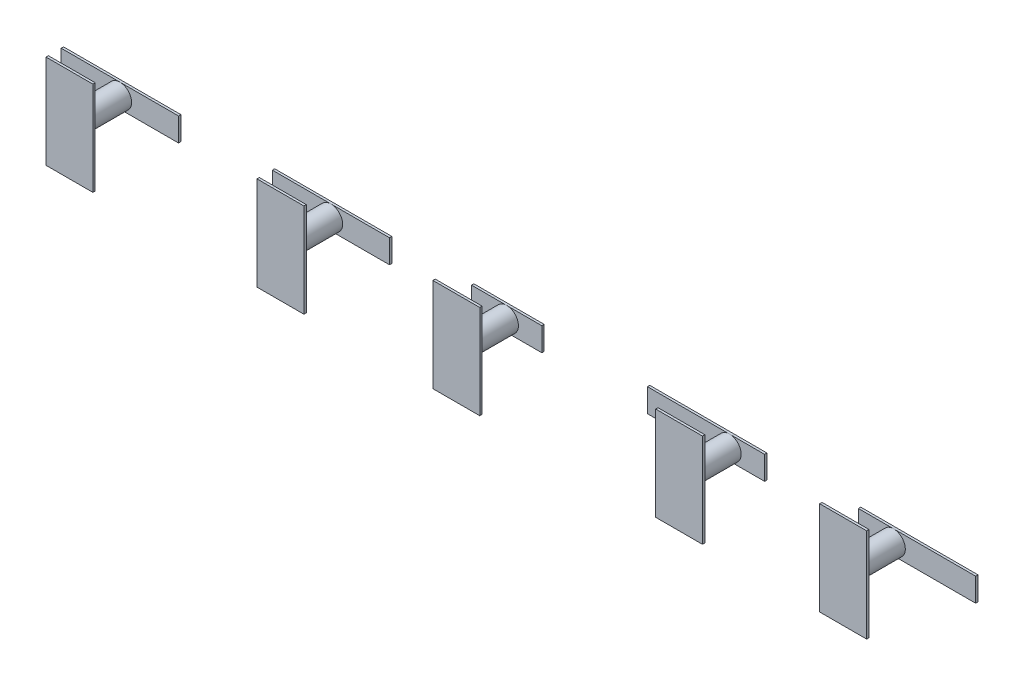
SolidWorks part; units mm, degrees
ref_plane "Front Plane" through (0, 0, 0) normal (0, 0, 1) x (1, 0, 0)
ref_plane "Top Plane" through (0, 0, 0) normal (0, 1, 0) x (1, 0, 0)
ref_plane "Right Plane" through (0, 0, 0) normal (1, 0, 0) x (0, 0, -1)
sketch "Sketch1" plane through (0, 0, 0) normal (0, 0, 1) x (1, 0, 0)
  line L1 (-61, 40) -> (61, 40)
  line L2 (-63, 38) -> (-63, -38)
  line L3 (-61, -40) -> (61, -40)
  line L4 (63, 38) -> (63, -38)
  line L5 (-63, 40) -> (63, -40) construction
  line L6 (-63, -40) -> (63, 40) construction
  arc A0 (61, 40) -> (63, 38) centre (61, 38) cw
  arc A1 (63, -38) -> (61, -40) centre (61, -38) cw
  arc A2 (-61, -40) -> (-63, -38) centre (-61, -38) cw
  arc A3 (-63, 38) -> (-61, 40) centre (-61, 38) cw
  point P0 (0, 0)
  dimension "D1" = 2
sketch "Sketch2" plane through (0, 0, 0) normal (0, 0, 1) x (1, 0, 0)
  line L0 (-5, 5.1169) -> (-5, -5.1169)
  line L1 (-4.2428, -5.5457) -> (4.2854, -0.4287)
  line L2 (4.2854, 0.4287) -> (-4.2428, 5.5457)
  line L3 (-10, -1.5) -> (-10, 1.5)
  line L4 (-10.5, 2) -> (-14, 2)
  line L5 (-14, 2) -> (-14, 5.5)
  line L6 (-14.5, 6) -> (-17.5, 6)
  line L7 (-18, 5.5) -> (-18, 2)
  line L8 (-18, 2) -> (-21.5, 2)
  line L9 (-22, 1.5) -> (-22, -1.5)
  line L10 (-21.5, -2) -> (-18, -2)
  line L11 (-18, -2) -> (-18, -5.5)
  line L12 (-17.5, -6) -> (-14.5, -6)
  line L13 (-14, -5.5) -> (-14, -2)
  line L14 (-14, -2) -> (-10.5, -2)
  line L15 (-28, 1.5) -> (-28, -1.5)
  line L16 (-28.5, -2) -> (-39.5, -2)
  line L17 (-40, -1.5) -> (-40, 1.5)
  line L18 (-39.5, 2) -> (-28.5, 2)
  line L19 (10, 4.5) -> (10, -4.5)
  line L20 (10.5, -5) -> (12.5, -5)
  line L21 (13, -4.5) -> (13, -2)
  line L22 (12.5, 5) -> (10.5, 5)
  line L23 (28, 5.2306) -> (28, -5.2306)
  line L24 (21.2969, 5.6875) -> (13, 2)
  line L25 (13, -2) -> (21.2969, -5.6875)
  line L26 (22, -5.2306) -> (22, 5.2306)
  line L27 (13, 2) -> (13, 4.5)
  line L28 (28.7031, -5.6875) -> (37, -2)
  line L29 (28.7031, 5.6875) -> (37, 2)
  line L30 (37, 2) -> (37, 4.5)
  line L31 (37.5, 5) -> (39.5, 5)
  line L32 (40, 4.5) -> (40, -4.5)
  line L33 (39.5, -5) -> (37.5, -5)
  line L34 (37, -4.5) -> (37, -2)
  arc A0 (-39.5, -2) -> (-40, -1.5) centre (-39.5, -1.5) cw
  arc A1 (-40, 1.5) -> (-39.5, 2) centre (-39.5, 1.5) cw
  arc A2 (-28.5, 2) -> (-28, 1.5) centre (-28.5, 1.5) cw
  arc A3 (-28, -1.5) -> (-28.5, -2) centre (-28.5, -1.5) cw
  arc A4 (-14.5, -6) -> (-14, -5.5) centre (-14.5, -5.5) ccw
  arc A5 (-17.5, -6) -> (-18, -5.5) centre (-17.5, -5.5) cw
  arc A6 (-21.5, -2) -> (-22, -1.5) centre (-21.5, -1.5) cw
  arc A7 (-22, 1.5) -> (-21.5, 2) centre (-21.5, 1.5) cw
  arc A8 (-18, 5.5) -> (-17.5, 6) centre (-17.5, 5.5) cw
  arc A9 (-14.5, 6) -> (-14, 5.5) centre (-14.5, 5.5) cw
  arc A10 (-10.5, 2) -> (-10, 1.5) centre (-10.5, 1.5) cw
  arc A11 (-10.5, -2) -> (-10, -1.5) centre (-10.5, -1.5) ccw
  arc A12 (-4.2428, -5.5457) -> (-5, -5.1169) centre (-4.5, -5.1169) cw
  arc A13 (-5, 5.1169) -> (-4.2428, 5.5457) centre (-4.5, 5.1169) cw
  arc A14 (4.2854, -0.4287) -> (4.2854, 0.4287) centre (4.0282, 0) ccw
  arc A15 (21.2969, 5.6875) -> (22, 5.2306) centre (21.5, 5.2306) cw
  arc A16 (22, -5.2306) -> (21.2969, -5.6875) centre (21.5, -5.2306) cw
  arc A17 (12.5, -5) -> (13, -4.5) centre (12.5, -4.5) ccw
  arc A18 (10.5, -5) -> (10, -4.5) centre (10.5, -4.5) cw
  arc A19 (10, 4.5) -> (10.5, 5) centre (10.5, 4.5) cw
  arc A20 (12.5, 5) -> (13, 4.5) centre (12.5, 4.5) cw
  arc A21 (28.7031, -5.6875) -> (28, -5.2306) centre (28.5, -5.2306) cw
  arc A22 (28, 5.2306) -> (28.7031, 5.6875) centre (28.5, 5.2306) cw
  arc A23 (37.5, -5) -> (37, -4.5) centre (37.5, -4.5) cw
  arc A24 (39.5, -5) -> (40, -4.5) centre (39.5, -4.5) ccw
  arc A25 (37, 4.5) -> (37.5, 5) centre (37.5, 4.5) cw
  arc A26 (40, 4.5) -> (39.5, 5) centre (39.5, 4.5) ccw
  dimension "D1" = 0.5
sketch "Sketch5" plane through (0, 0, 0) normal (0, 0, 1) x (1, 0, 0)
  line L0 (-21, 1) -> (-17, 1)
  line L1 (-39, 1) -> (-29, 1)
  line L2 (-39, 1) -> (-39, -1)
  line L3 (-39, -1) -> (-29, -1)
  line L4 (-29, 1) -> (-29, -1)
  line L5 (-17, 1) -> (-17, 5)
  line L6 (-17, 5) -> (-15, 5)
  line L7 (-15, 5) -> (-15, 1)
  line L8 (-15, 1) -> (-11, 1)
  line L9 (-11, 1) -> (-11, -1)
  line L10 (-11, -1) -> (-15, -1)
  line L11 (-15, -1) -> (-15, -5)
  line L12 (-15, -5) -> (-17, -5)
  line L13 (-17, -5) -> (-17, -1)
  line L14 (-17, -1) -> (-21, -1)
  line L15 (-21, -1) -> (-21, 1)
  line L16 (-4, 4) -> (-4, -4)
  line L17 (-4, -4) -> (3, 0)
  line L18 (3, 0) -> (-4, 4)
  line L19 (29, 4) -> (29, -4)
  line L20 (29, -4) -> (39, 0)
  line L21 (39, 0) -> (29, 4)
  line L22 (11, 0) -> (21, -4)
  line L23 (21, -4) -> (21, 4)
  line L24 (21, 4) -> (11, 0)
ref_plane "Plane2" through (0, 0, 0.5) normal (0, 0, 1) x (1, 0, 0)
sketch "Sketch8" plane through (0, 0, 0.5) normal (0, 0, 1) x (1, 0, 0)
  line L0 (-21, 1) -> (-17, 1)
  line L1 (-39, 1) -> (-29, 1)
  line L2 (-39, 1) -> (-39, -1)
  line L3 (-39, -1) -> (-29, -1)
  line L4 (-29, 1) -> (-29, -1)
  line L6 (-4, 4) -> (-4, -4) construction
  line L7 (-4, 1) -> (2, 1)
  line L8 (-17, 1) -> (-11, 1)
  line L9 (-11, 1) -> (-11, -1)
  line L10 (-11, -1) -> (-17, -1)
  line L11 (-4, 1) -> (-4, -1)
  line L12 (-4, -1) -> (2, -1)
  line L13 (2, 1) -> (2, -1)
  line L14 (-17, -1) -> (-21, -1)
  line L15 (-21, -1) -> (-21, 1)
  line L16 (21, -4) -> (21, 4) construction
  line L17 (11, 1) -> (21, 1)
  line L18 (11, 1) -> (11, -1)
  line L19 (11, -1) -> (21, -1)
  line L20 (21, 1) -> (21, -1)
  line L21 (29, 4) -> (29, -4) construction
  line L22 (29, 1) -> (39, 1)
  line L23 (29, 1) -> (29, -1)
  line L24 (29, -1) -> (39, -1)
  line L25 (39, 1) -> (39, -1)
ref_plane "Plane3" through (0, 0, 5) normal (0, 0, 1) x (1, 0, 0)
sketch "Sketch9" plane through (0, 0, 5) normal (0, 0, 1) x (1, 0, 0)
  circle A0 centre (-34, 0) radius 1
  circle A1 centre (-16, 0) radius 1
  circle A2 centre (-1, 0) radius 1
  circle A3 centre (18, 0) radius 1
  circle A4 centre (32, 0) radius 1
sketch "Sketch10" plane through (0, 0, 5) normal (0, 0, 1) x (1, 0, 0)
  circle A0 centre (-34, 0) radius 1
  circle A1 centre (-16, 0) radius 1
  circle A2 centre (-1, 0) radius 1
  circle A3 centre (18, 0) radius 1
  circle A4 centre (32, 0) radius 1
sketch "Sketch11" plane through (0, 0, 5) normal (0, 0, 1) x (1, 0, 0)
  line L1 (-36, 4) -> (-32, 4)
  line L2 (-36, 4) -> (-36, -4)
  line L3 (-36, -4) -> (-32, -4)
  line L4 (-32, 4) -> (-32, -4)
  line L5 (-18, 4) -> (-14, 4)
  line L6 (-18, 4) -> (-18, -4)
  line L7 (-18, -4) -> (-14, -4)
  line L8 (-14, 4) -> (-14, -4)
  line L9 (-3, 4) -> (1, 4)
  line L10 (-3, 4) -> (-3, -4)
  line L11 (-3, -4) -> (1, -4)
  line L12 (1, 4) -> (1, -4)
  line L13 (16, 4) -> (20, 4)
  line L14 (16, 4) -> (16, -4)
  line L15 (16, -4) -> (20, -4)
  line L16 (20, 4) -> (20, -4)
  line L17 (30, 4) -> (34, 4)
  line L18 (30, 4) -> (30, -4)
  line L19 (30, -4) -> (34, -4)
  line L20 (34, 4) -> (34, -4)
sketch "Sketch12" plane through (0, 0, 5) normal (0, 0, 1) x (1, 0, 0)
  circle A0 centre (-45, 0) radius 1.25
  circle A1 centre (45, 0) radius 1.25
  circle A2 centre (0, 10) radius 1.25
  circle A3 centre (0, -10) radius 1.25
sketch "Sketch13" plane through (0, 0, 5) normal (0, 0, 1) x (1, 0, 0)
  circle A0 centre (60, 37) radius 1
  circle A1 centre (60, -37) radius 1
  circle A2 centre (-60, -37) radius 1
  circle A3 centre (-60, 37) radius 1
  circle A4 centre (0, 37) radius 1
  circle A5 centre (0, -37) radius 1
  circle A6 centre (-60, 0) radius 1
  circle A7 centre (60, 0) radius 1
sketch "Sketch14" plane through (0, 0, 0.5) normal (0, 0, 1) x (1, 0, 0)
  line L0 (-21, 1) -> (-17, 1)
  line L1 (-39, 1) -> (-29, 1)
  line L2 (-39, 1) -> (-39, -1)
  line L3 (-39, -1) -> (-29, -1)
  line L4 (-29, 1) -> (-29, -1)
  line L5 (-17, 1) -> (-17, 5)
  line L6 (-17, 5) -> (-15, 5)
  line L7 (-15, 5) -> (-15, 1)
  line L8 (-15, 1) -> (-11, 1)
  line L9 (-11, 1) -> (-11, -1)
  line L10 (-11, -1) -> (-15, -1)
  line L11 (-15, -1) -> (-15, -5)
  line L12 (-15, -5) -> (-17, -5)
  line L13 (-17, -5) -> (-17, -1)
  line L14 (-17, -1) -> (-21, -1)
  line L15 (-21, -1) -> (-21, 1)
  line L16 (-4, 4) -> (-4, -4)
  line L17 (-4, -4) -> (3, 0)
  line L18 (3, 0) -> (-4, 4)
  line L19 (29, 4) -> (29, -4)
  line L20 (29, -4) -> (39, 0)
  line L21 (39, 0) -> (29, 4)
  line L22 (11, 0) -> (21, -4)
  line L23 (21, -4) -> (21, 4)
  line L24 (21, 4) -> (11, 0)
extrude "Boss-Extrude1" add sketch "Sketch8" along normal blind 0.2
extrude "Boss-Extrude2" add sketch "Sketch10" against normal blind 4.5 separate body
extrude "Boss-Extrude3" add sketch "Sketch11" against normal blind 0.2
